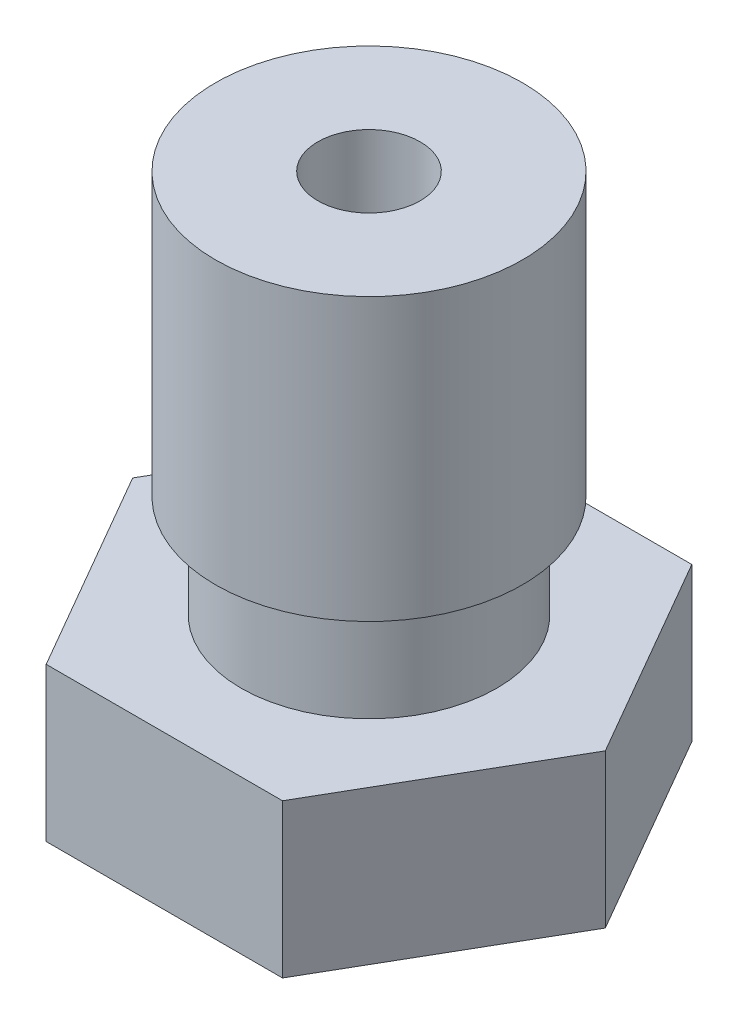
SolidWorks part; units mm, degrees
material "Brass"
ref_plane "Front Plane" through (0, 0, 0) normal (0, 0, 1) x (1, 0, 0)
ref_plane "Top Plane" through (0, 0, 0) normal (0, 1, 0) x (1, 0, 0)
ref_plane "Right Plane" through (0, 0, 0) normal (1, 0, 0) x (0, 0, -1)
sketch "Sketch1" plane through (0, 0, 0) normal (0, 1, 0) x (1, 0, 0)
  line L1 (2.3094, 4) -> (-2.3094, 4)
  line L2 (-2.3094, 4) -> (-4.6188, 0)
  line L3 (-4.6188, 0) -> (-2.3094, -4)
  line L4 (-2.3094, -4) -> (2.3094, -4)
  line L5 (2.3094, -4) -> (4.6188, 0)
  line L6 (4.6188, 0) -> (2.3094, 4)
  circle A0 centre (0, 0) radius 4 construction
  circle A1 centre (0, 0) radius 1
  dimension "D2" = 2
  dimension "D1" = 8
extrude "Boss-Extrude1" add sketch "Sketch1" along normal blind 3
sketch "Sketch2" plane through (0, 0, 0) normal (0, 0, 1) x (1, 0, 0)
  line L0 (1, 0) -> (0.225, -2)
  line L1 (-2.3094, 0) -> (2.3094, 0) construction
  line L2 (0.225, -2) -> (0.6, -2)
  line L3 (0.6, -2) -> (2.0004, 0)
  line L4 (2.3094, 0) -> (4.6188, 0) construction
  line L5 (0, -2) -> (0, 8.8072) construction
  line L6 (1, 0) -> (2.0004, 0)
  line L7 (1, 3) -> (1, 10.5)
  line L8 (-2.3094, 3) -> (2.3094, 3) construction
  line L9 (1, 10.5) -> (3, 10.5)
  line L10 (3, 10.5) -> (3, 5)
  line L11 (3, 5) -> (2.5, 5)
  line L12 (2.5, 5) -> (2.5, 3)
  line L13 (2.3094, 3) -> (4.6188, 3) construction
  line L14 (2.5, 3) -> (1, 3)
  line L15 (1, 3) -> (1.0359, 2.9796)
  dimension "D1" = 0.6
  dimension "D2" = 2
  dimension "D3" = 0.225
  dimension "D4" = 125
  dimension "D6" = 6
  dimension "D7" = 5.5
  dimension "D8" = 0.5
  dimension "D9" = 2
revolve "Revolve1" add sketch "Sketch2" angle 360 about L5
